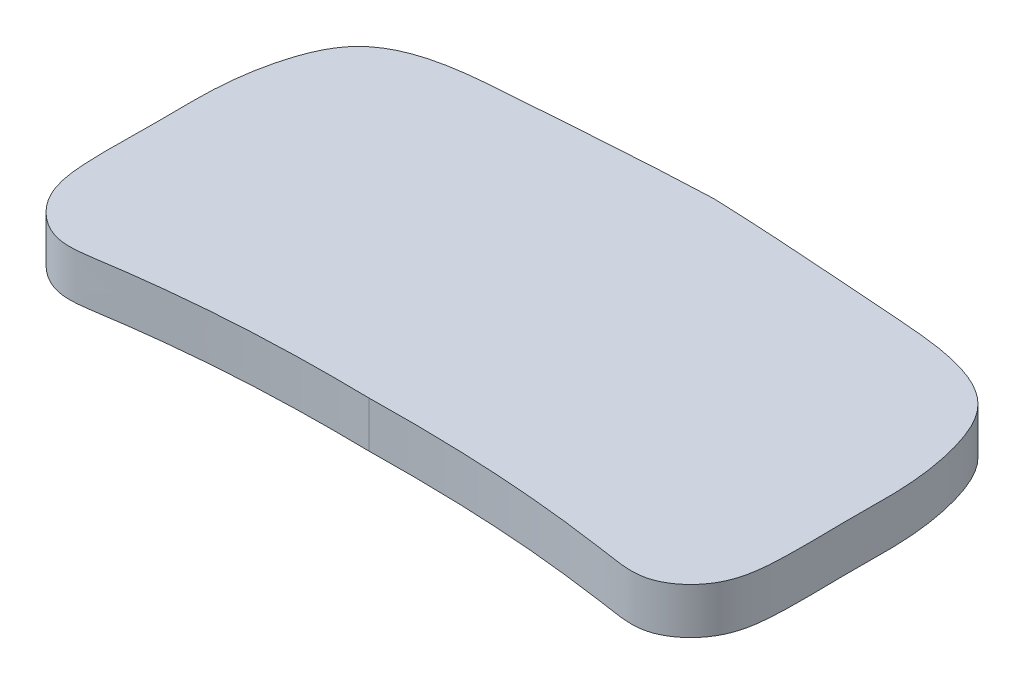
SolidWorks part; units mm, degrees
ref_plane "Ön Düzlem" through (0, 0, 0) normal (0, 0, 1) x (1, 0, 0)
ref_plane "Üst Düzlem" through (0, 0, 0) normal (0, 1, 0) x (1, 0, 0)
ref_plane "Sağ Düzlem" through (0, 0, 0) normal (1, 0, 0) x (0, 0, -1)
sketch "Çizim1" plane through (0, 0, 0) normal (0, 1, 0) x (1, 0, 0)
  line L0 (0, 17.9288) -> (0, -12.0712) construction
  line L1 (0, 0) -> (-30, 0) construction
  line L2 (-108.3091, -42.1463) -> (-63.9653, -42.1463) construction
  spline S0 degree 3 poles (0, 17.9288) (-5.8202, 17.7095) (-13.9034, 17.0426) (-26.8757, 16.196) (-29.5503, 8.9293) (-30.0905, 4.3361) (-29.9407, -0.8874) (-30.1549, -5.7017) (-29.6372, -10.9288) (-26.0312, -14.0818) (-15.7201, -12.3493) (-7.8072, -11.9389) (0, -12.0712) knots 0 0 0 0 0.19846 0.336013 0.394477 0.45973 0.505377 0.582751 0.635933 0.690009 0.731881 1 1 1 1
  spline S1 degree 3 poles (0, 17.9288) (5.8202, 17.7095) (13.9034, 17.0426) (26.8757, 16.196) (29.5503, 8.9293) (30.0905, 4.3361) (29.9407, -0.8874) (30.1549, -5.7017) (29.6372, -10.9288) (26.0312, -14.0818) (15.7201, -12.3493) (7.8072, -11.9389) (0, -12.0712) knots 0 0 0 0 0.19846 0.336013 0.394477 0.45973 0.505377 0.582751 0.635933 0.690009 0.731881 1 1 1 1
  dimension "D1" = 30
  dimension "D2" = 30
extrude "Yükseklik-Ekstrüzyon1" add sketch "Çizim1" along normal blind 4
